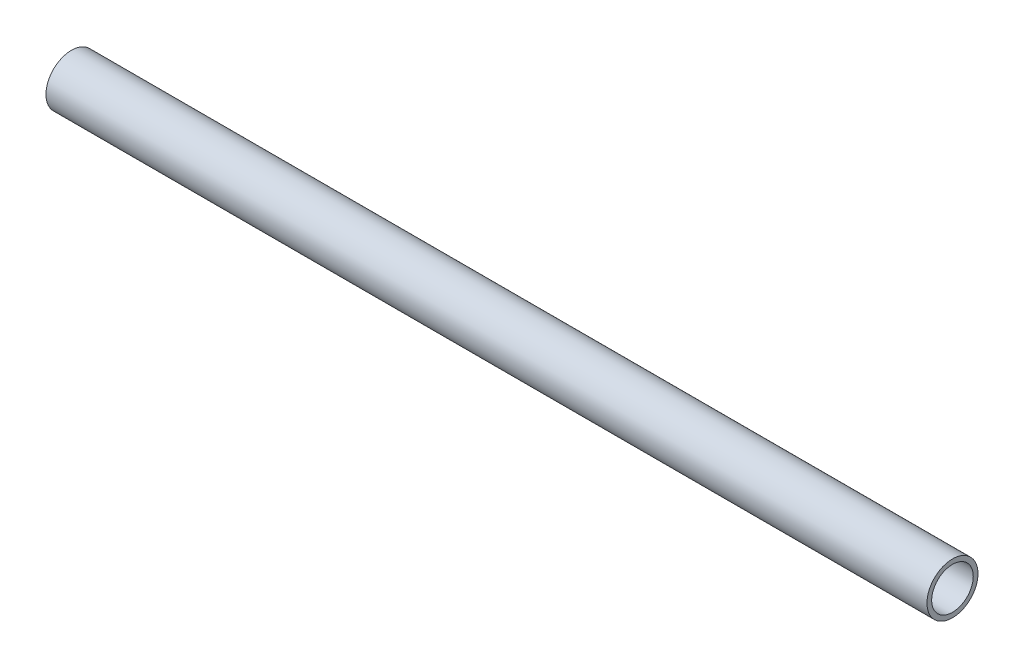
SolidWorks part; units mm, degrees
ref_plane "Front" through (0, 0, 0) normal (0, 0, 1) x (1, 0, 0)
ref_plane "Top" through (0, 0, 0) normal (0, 1, 0) x (1, 0, 0)
ref_plane "Right" through (0, 0, 0) normal (1, 0, 0) x (0, 0, -1)
sketch "Sketch1" plane through (0, 0, 0) normal (0, 0, 1) x (1, 0, 0)
  line L0 (0, 0) -> (273.9898, 0)
  dimension "D1" = 273.9898
other "Structural Member1"
ref_plane "Plane1" through (0, 0, 0) normal (1, 0, 0) x (0, 1, 0)
sketch "Sketch11" plane through (0, 0, 0) normal (1, 0, 0) x (0, 1, 0)
  circle A0 centre (0, 0) radius 6.4643
  circle A1 centre (0, 0) radius 7.9375
  point P5 (0, 0)
  dimension "Out_dia" = 15.875
  dimension "D1" = 1.4732
